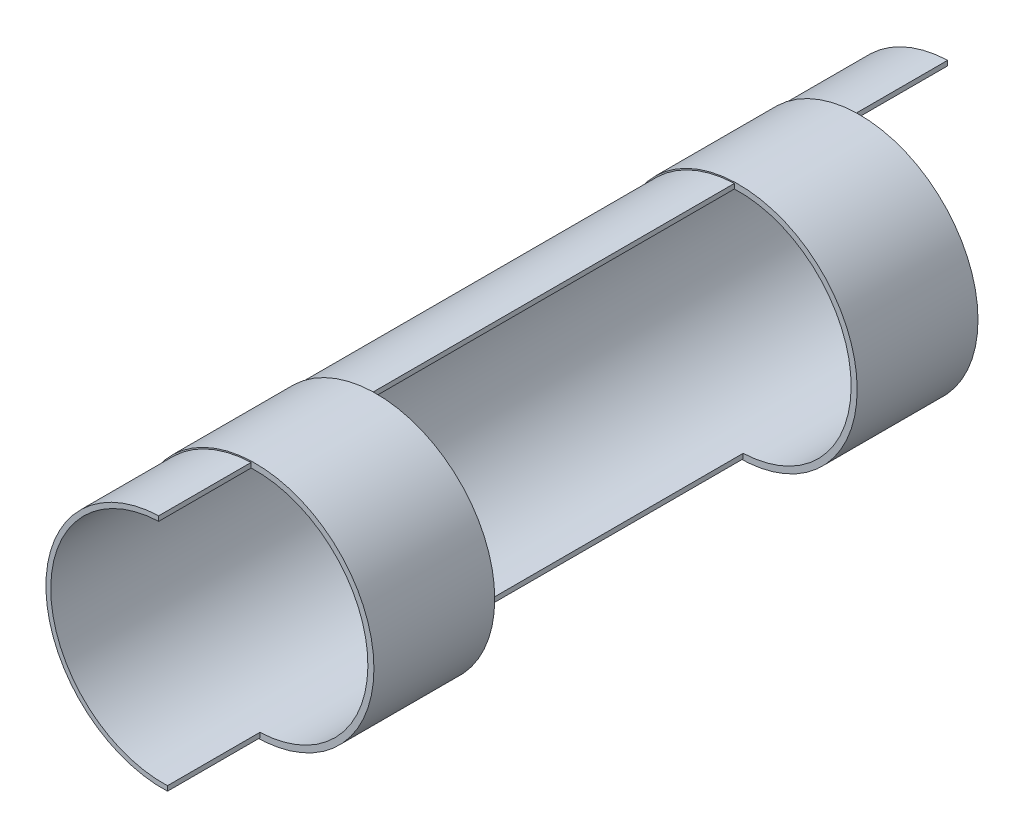
SolidWorks part; units mm, degrees
material "ABS PC"
ref_plane "Front Plane" through (0, 0, 0) normal (0, 0, 1) x (1, 0, 0)
ref_plane "Top Plane" through (0, 0, 0) normal (0, 1, 0) x (1, 0, 0)
ref_plane "Right Plane" through (0, 0, 0) normal (1, 0, 0) x (0, 0, -1)
sketch "Sketch1" plane through (0, 0, 0) normal (0, 0, 1) x (1, 0, 0)
  line L0 (-0.3618, 9.6933) -> (-0.3618, 9.293)
  line L1 (0.3618, -9.293) -> (0.3618, -9.6933)
  arc A0 (-0.3618, 9.6933) -> (0.3618, -9.6933) centre (0, 0) ccw
  arc A1 (-0.3618, 9.293) -> (0.3618, -9.293) centre (0, 0) ccw
  dimension "D1" = 9.3
  dimension "D2" = 9.7
extrude "Boss-Extrude1" add sketch "Sketch1" along normal mid plane 65.3 contours A1 L1 A0 L0
ref_plane "Plane1" through (0, 0, 20) normal (0, 0, 1) x (1, 0, 0)
sketch "Sketch2" plane through (0, 0, 20) normal (0, 0, 1) x (1, 0, 0)
  circle A0 centre (0, 0) radius 9.3
  circle A1 centre (0, 0) radius 9.8
  dimension "D1" = 18.6
  dimension "D2" = 19.6
extrude "Boss-Extrude2" add sketch "Sketch2" along normal mid plane 10 contours A0
pattern_linear "LPattern1" count 2 spacing 40 along (0, 0, -1) of "Boss-Extrude2"
